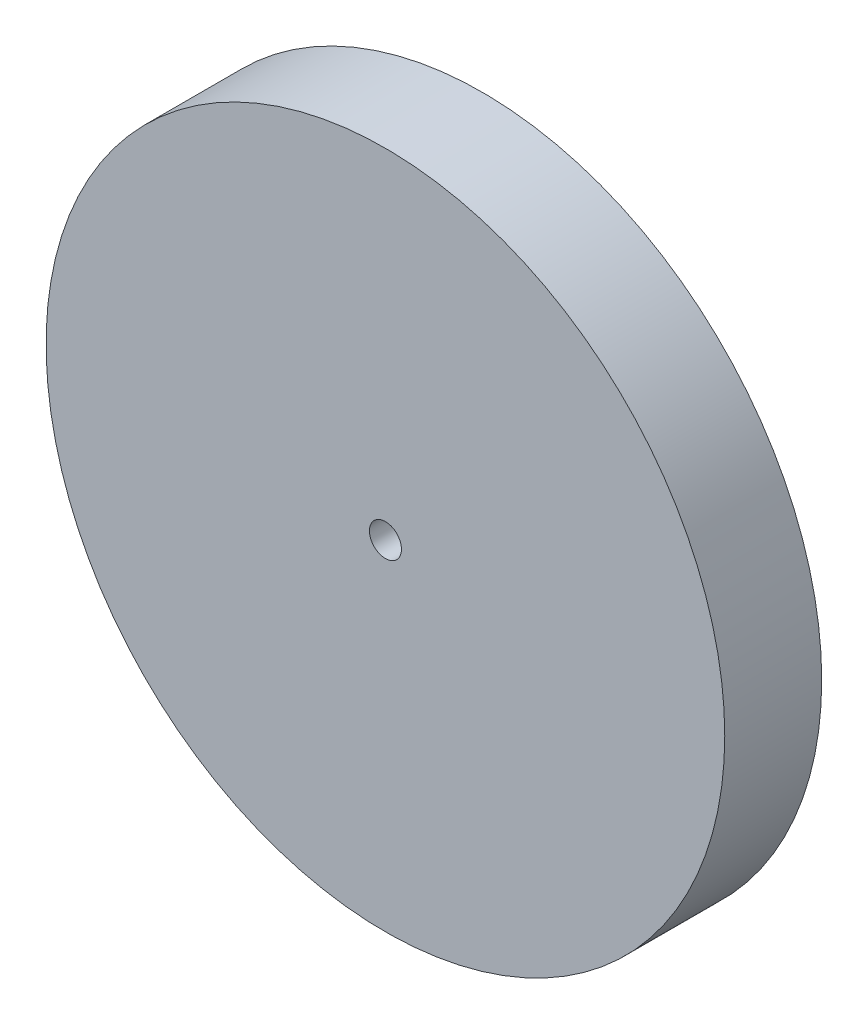
SolidWorks part; units mm, degrees
ref_plane "Front Plane" through (0, 0, 0) normal (0, 0, 1) x (1, 0, 0)
ref_plane "Top Plane" through (0, 0, 0) normal (0, 1, 0) x (1, 0, 0)
ref_plane "Right Plane" through (0, 0, 0) normal (1, 0, 0) x (0, 0, -1)
sketch "Sketch1" plane through (0, 0, 0) normal (0, 0, 1) x (1, 0, 0)
  circle A0 centre (0, 0) radius 35
extrude "Boss-Extrude1" add sketch "Sketch1" along normal blind 10
sketch "Sketch2" plane through (0, 0, 0) normal (0, 0, -1) x (-1, 0, 0)
  circle A0 centre (0, 0) radius 1.5
extrude "Boss-Extrude2" add sketch "Sketch2" along normal blind 5
sketch "Sketch3" plane through (0, 0, 10) normal (0, 0, 1) x (1, 0, 0)
  circle A0 centre (0, 0) radius 1.65
extrude "Cut-Extrude1" cut sketch "Sketch3" against normal blind 5
